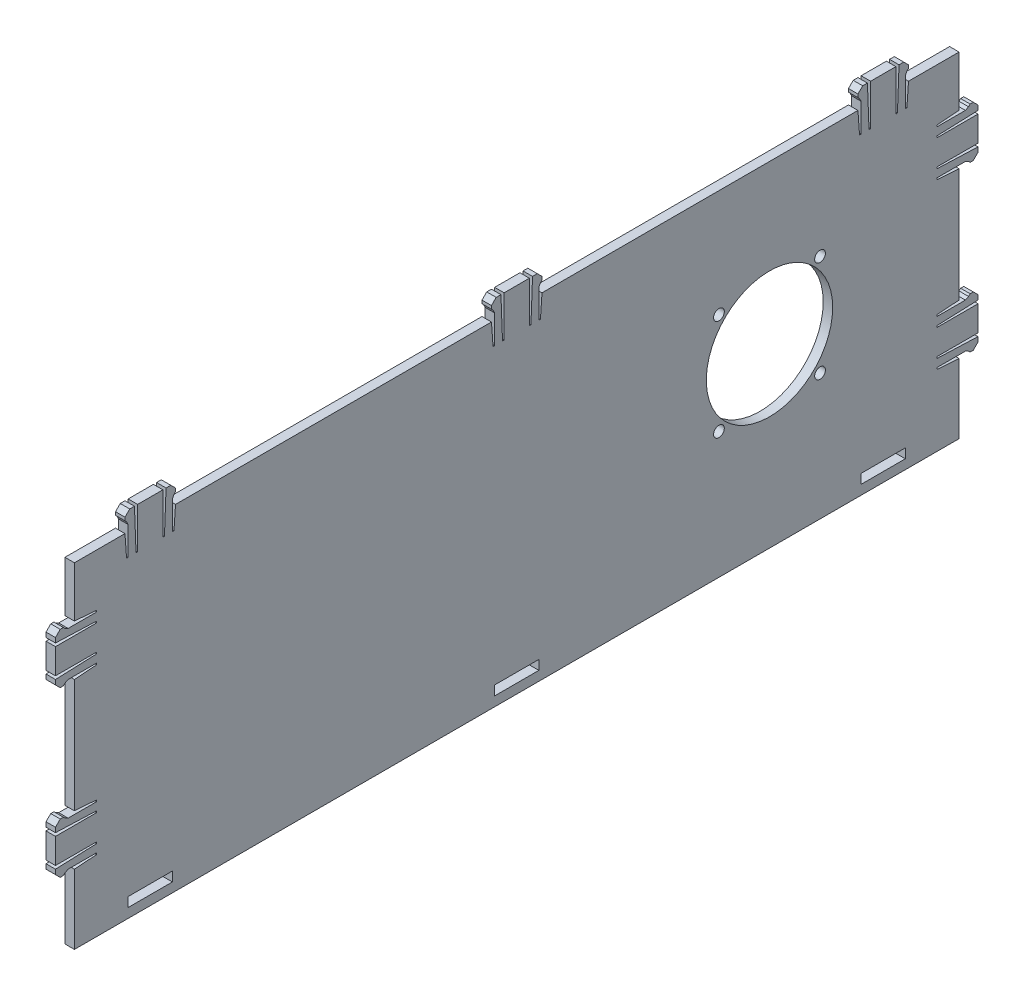
SolidWorks part; units mm, degrees
ref_plane "Front Plane" through (0, 0, 0) normal (0, 0, 1) x (1, 0, 0)
ref_plane "Top Plane" through (0, 0, 0) normal (0, 1, 0) x (1, 0, 0)
ref_plane "Right Plane" through (0, 0, 0) normal (1, 0, 0) x (0, 0, -1)
sketch "Sketch1" plane through (0, 0, 0) normal (1, 0, 0) x (0, 0, -1)
  line L0 (-140, 34) -> (-140, 50)
  line L1 (-124, 50) -> (-140, 50)
  line L2 (-140, -34) -> (-140, -56)
  line L3 (-140, -56) -> (140, -56)
  line L4 (140, 34) -> (140, 50)
  line L5 (-140, 18) -> (-140, -18)
  line L6 (-140, -34) -> (-132.9978, -33.5)
  line L7 (-132.9978, -33.5) -> (-132.9978, -33)
  line L8 (-132.9978, -33) -> (-141.9978, -33)
  line L9 (-141.9978, -33) -> (-142.9978, -33.5)
  line L10 (-142.9978, -33.5) -> (-143.4978, -34)
  line L11 (-143.4978, -34) -> (-144.4978, -34)
  line L12 (-144.4978, -34) -> (-145.9978, -32.5)
  line L13 (-145.9978, -32.5) -> (-145.9978, -31)
  line L14 (-145.9978, -31) -> (-132.9978, -30.5)
  line L15 (-132.9978, -30.5) -> (-132.9978, -30)
  line L16 (-132.9978, -30) -> (-145.9978, -30)
  line L17 (-132.9978, -22) -> (-145.9978, -22)
  line L18 (-132.9978, -21.5) -> (-132.9978, -22)
  line L19 (-145.9978, -21) -> (-132.9978, -21.5)
  line L20 (-145.9978, -19.5) -> (-145.9978, -21)
  line L21 (-144.4978, -18) -> (-145.9978, -19.5)
  line L22 (-143.4978, -18) -> (-144.4978, -18)
  line L23 (-142.9978, -18.5) -> (-143.4978, -18)
  line L24 (-141.9978, -19) -> (-142.9978, -18.5)
  line L25 (-132.9978, -19) -> (-141.9978, -19)
  line L26 (-132.9978, -18.5) -> (-132.9978, -19)
  line L27 (-140, -18) -> (-132.9978, -18.5)
  line L28 (-145.9978, -30) -> (-145.9978, -22)
  line L29 (-140, 18) -> (-132.9978, 18.5)
  line L30 (-132.9978, 18.5) -> (-132.9978, 19)
  line L31 (-132.9978, 19) -> (-141.9978, 19)
  line L32 (-141.9978, 19) -> (-142.9978, 18.5)
  line L33 (-142.9978, 18.5) -> (-143.4978, 18)
  line L34 (-143.4978, 18) -> (-144.4978, 18)
  line L35 (-144.4978, 18) -> (-145.9978, 19.5)
  line L36 (-145.9978, 19.5) -> (-145.9978, 21)
  line L37 (-145.9978, 21) -> (-132.9978, 21.5)
  line L38 (-132.9978, 21.5) -> (-132.9978, 22)
  line L39 (-132.9978, 22) -> (-145.9978, 22)
  line L40 (-132.9978, 30) -> (-145.9978, 30)
  line L41 (-132.9978, 30.5) -> (-132.9978, 30)
  line L42 (-145.9978, 31) -> (-132.9978, 30.5)
  line L43 (-145.9978, 32.5) -> (-145.9978, 31)
  line L44 (-144.4978, 34) -> (-145.9978, 32.5)
  line L45 (-143.4978, 34) -> (-144.4978, 34)
  line L46 (-142.9978, 33.5) -> (-143.4978, 34)
  line L47 (-141.9978, 33) -> (-142.9978, 33.5)
  line L48 (-132.9978, 33) -> (-141.9978, 33)
  line L49 (-132.9978, 33.5) -> (-132.9978, 33)
  line L50 (-140, 34) -> (-132.9978, 33.5)
  line L51 (-145.9978, 22) -> (-145.9978, 30)
  line L52 (140, -34) -> (140, -56)
  line L53 (140, -18) -> (140, 18)
  line L54 (140, 34) -> (132.9978, 33.5)
  line L55 (132.9978, 33.5) -> (132.9978, 33)
  line L56 (132.9978, 33) -> (141.9978, 33)
  line L57 (141.9978, 33) -> (142.9978, 33.5)
  line L58 (142.9978, 33.5) -> (143.4978, 34)
  line L59 (143.4978, 34) -> (144.4978, 34)
  line L60 (144.4978, 34) -> (145.9978, 32.5)
  line L61 (145.9978, 32.5) -> (145.9978, 31)
  line L62 (145.9978, 31) -> (132.9978, 30.5)
  line L63 (132.9978, 30.5) -> (132.9978, 30)
  line L64 (132.9978, 30) -> (145.9978, 30)
  line L65 (132.9978, 22) -> (145.9978, 22)
  line L66 (132.9978, 21.5) -> (132.9978, 22)
  line L67 (145.9978, 21) -> (132.9978, 21.5)
  line L68 (145.9978, 19.5) -> (145.9978, 21)
  line L69 (144.4978, 18) -> (145.9978, 19.5)
  line L70 (143.4978, 18) -> (144.4978, 18)
  line L71 (142.9978, 18.5) -> (143.4978, 18)
  line L72 (141.9978, 19) -> (142.9978, 18.5)
  line L73 (132.9978, 19) -> (141.9978, 19)
  line L74 (132.9978, 18.5) -> (132.9978, 19)
  line L75 (140, 18) -> (132.9978, 18.5)
  line L76 (145.9978, 30) -> (145.9978, 22)
  line L77 (140, -18) -> (132.9978, -18.5)
  line L78 (132.9978, -18.5) -> (132.9978, -19)
  line L79 (132.9978, -19) -> (141.9978, -19)
  line L80 (141.9978, -19) -> (142.9978, -18.5)
  line L81 (142.9978, -18.5) -> (143.4978, -18)
  line L82 (143.4978, -18) -> (144.4978, -18)
  line L83 (144.4978, -18) -> (145.9978, -19.5)
  line L84 (145.9978, -19.5) -> (145.9978, -21)
  line L85 (145.9978, -21) -> (132.9978, -21.5)
  line L86 (132.9978, -21.5) -> (132.9978, -22)
  line L87 (132.9978, -22) -> (145.9978, -22)
  line L88 (132.9978, -30) -> (145.9978, -30)
  line L89 (132.9978, -30.5) -> (132.9978, -30)
  line L90 (145.9978, -31) -> (132.9978, -30.5)
  line L91 (145.9978, -32.5) -> (145.9978, -31)
  line L92 (144.4978, -34) -> (145.9978, -32.5)
  line L93 (143.4978, -34) -> (144.4978, -34)
  line L94 (142.9978, -33.5) -> (143.4978, -34)
  line L95 (141.9978, -33) -> (142.9978, -33.5)
  line L96 (132.9978, -33) -> (141.9978, -33)
  line L97 (132.9978, -33.5) -> (132.9978, -33)
  line L98 (140, -34) -> (132.9978, -33.5)
  line L99 (145.9978, -22) -> (145.9978, -30)
  line L100 (124, 50) -> (140, 50)
  line L101 (-108, 50) -> (-8, 50)
  line L102 (8, 50) -> (108, 50)
  line L103 (-124, 50) -> (-123.5, 42.9978)
  line L104 (-123.5, 42.9978) -> (-123, 42.9978)
  line L105 (-123, 42.9978) -> (-123, 51.9978)
  line L106 (-123, 51.9978) -> (-123.5, 52.9978)
  line L107 (-123.5, 52.9978) -> (-124, 53.4978)
  line L108 (-124, 53.4978) -> (-124, 54.4978)
  line L109 (-124, 54.4978) -> (-122.5, 55.9978)
  line L110 (-122.5, 55.9978) -> (-121, 55.9978)
  line L111 (-121, 55.9978) -> (-120.5, 42.9978)
  line L112 (-120.5, 42.9978) -> (-120, 42.9978)
  line L113 (-120, 42.9978) -> (-120, 55.9978)
  line L114 (-116, 50) -> (-116, 55.7386) construction
  line L115 (-112, 42.9978) -> (-112, 55.9978)
  line L116 (-111.5, 42.9978) -> (-112, 42.9978)
  line L117 (-111, 55.9978) -> (-111.5, 42.9978)
  line L118 (-109.5, 55.9978) -> (-111, 55.9978)
  line L119 (-108, 54.4978) -> (-109.5, 55.9978)
  line L120 (-108, 53.4978) -> (-108, 54.4978)
  line L121 (-108.5, 52.9978) -> (-108, 53.4978)
  line L122 (-109, 51.9978) -> (-108.5, 52.9978)
  line L123 (-109, 42.9978) -> (-109, 51.9978)
  line L124 (-108.5, 42.9978) -> (-109, 42.9978)
  line L125 (-108, 50) -> (-108.5, 42.9978)
  line L126 (-120, 55.9978) -> (-112, 55.9978)
  line L127 (-8, 50) -> (-7.5, 42.9978)
  line L128 (-7.5, 42.9978) -> (-7, 42.9978)
  line L129 (-7, 42.9978) -> (-7, 51.9978)
  line L130 (-7, 51.9978) -> (-7.5, 52.9978)
  line L131 (-7.5, 52.9978) -> (-8, 53.4978)
  line L132 (-8, 53.4978) -> (-8, 54.4978)
  line L133 (-8, 54.4978) -> (-6.5, 55.9978)
  line L134 (-6.5, 55.9978) -> (-5, 55.9978)
  line L135 (-5, 55.9978) -> (-4.5, 42.9978)
  line L136 (-4.5, 42.9978) -> (-4, 42.9978)
  line L137 (-4, 42.9978) -> (-4, 55.9978)
  line L138 (0, 50) -> (0, 55.7386) construction
  line L139 (4, 42.9978) -> (4, 55.9978)
  line L140 (4.5, 42.9978) -> (4, 42.9978)
  line L141 (5, 55.9978) -> (4.5, 42.9978)
  line L142 (6.5, 55.9978) -> (5, 55.9978)
  line L143 (8, 54.4978) -> (6.5, 55.9978)
  line L144 (8, 53.4978) -> (8, 54.4978)
  line L145 (7.5, 52.9978) -> (8, 53.4978)
  line L146 (7, 51.9978) -> (7.5, 52.9978)
  line L147 (7, 42.9978) -> (7, 51.9978)
  line L148 (7.5, 42.9978) -> (7, 42.9978)
  line L149 (8, 50) -> (7.5, 42.9978)
  line L150 (-4, 55.9978) -> (4, 55.9978)
  line L151 (108, 50) -> (108.5, 42.9978)
  line L152 (108.5, 42.9978) -> (109, 42.9978)
  line L153 (109, 42.9978) -> (109, 51.9978)
  line L154 (109, 51.9978) -> (108.5, 52.9978)
  line L155 (108.5, 52.9978) -> (108, 53.4978)
  line L156 (108, 53.4978) -> (108, 54.4978)
  line L157 (108, 54.4978) -> (109.5, 55.9978)
  line L158 (109.5, 55.9978) -> (111, 55.9978)
  line L159 (111, 55.9978) -> (111.5, 42.9978)
  line L160 (111.5, 42.9978) -> (112, 42.9978)
  line L161 (112, 42.9978) -> (112, 55.9978)
  line L162 (116, 50) -> (116, 55.7386) construction
  line L163 (120, 42.9978) -> (120, 55.9978)
  line L164 (120.5, 42.9978) -> (120, 42.9978)
  line L165 (121, 55.9978) -> (120.5, 42.9978)
  line L166 (122.5, 55.9978) -> (121, 55.9978)
  line L167 (124, 54.4978) -> (122.5, 55.9978)
  line L168 (124, 53.4978) -> (124, 54.4978)
  line L169 (123.5, 52.9978) -> (124, 53.4978)
  line L170 (123, 51.9978) -> (123.5, 52.9978)
  line L171 (123, 42.9978) -> (123, 51.9978)
  line L172 (123.5, 42.9978) -> (123, 42.9978)
  line L173 (124, 50) -> (123.5, 42.9978)
  line L174 (112, 55.9978) -> (120, 55.9978)
  point P12 (-140, -34)
  point P37 (-140, 18)
  point P61 (140, 34)
  point P62 (140, 18)
  point P63 (140, 18)
  point P86 (140, -18)
  point P87 (140, -34)
  point P88 (140, -34)
  point P117 (-124, 50)
  point P143 (-8, 50)
  point P168 (108, 50)
  dimension "D1" = 280
  dimension "D2" = 106
  dimension "D3" = 140
  dimension "D4" = 50
  dimension "D5" = 16
  dimension "D6" = 36
  dimension "D7" = 7.0022
  dimension "D8" = 0.5
  dimension "D9" = 0.5
  dimension "D10" = 9
  dimension "D11" = 1
  dimension "D12" = 0.5
  dimension "D13" = 0.5
  dimension "D14" = 0.5
  dimension "D15" = 1
  dimension "D16" = 1.5
  dimension "D17" = 1.5
  dimension "D18" = 1.5
  dimension "D19" = 13
  dimension "D20" = 0.5
  dimension "D21" = 0.5
  dimension "D22" = 13
  dimension "D23" = 8
  dimension "D24" = 13
  dimension "D25" = 0.5
  dimension "D26" = 13
  dimension "D27" = 0.5
  dimension "D28" = 1.5
  dimension "D29" = 1.5
  dimension "D30" = 1.5
  dimension "D31" = 1
  dimension "D32" = 0.5
  dimension "D33" = 0.5
  dimension "D34" = 1
  dimension "D35" = 0.5
  dimension "D36" = 9
  dimension "D37" = 0.5
  dimension "D38" = 7.0022
  dimension "D39" = 0.5
  dimension "D40" = 7.0022
  dimension "D41" = 0.5
  dimension "D42" = 0.5
  dimension "D43" = 9
  dimension "D44" = 1
  dimension "D45" = 0.5
  dimension "D46" = 0.5
  dimension "D47" = 0.5
  dimension "D48" = 1
  dimension "D49" = 1.5
  dimension "D50" = 1.5
  dimension "D51" = 1.5
  dimension "D52" = 13
  dimension "D53" = 0.5
  dimension "D54" = 0.5
  dimension "D55" = 13
  dimension "D56" = 8
  dimension "D57" = 13
  dimension "D58" = 0.5
  dimension "D59" = 13
  dimension "D60" = 0.5
  dimension "D61" = 1.5
  dimension "D62" = 1.5
  dimension "D63" = 1.5
  dimension "D64" = 1
  dimension "D65" = 0.5
  dimension "D66" = 0.5
  dimension "D67" = 1
  dimension "D68" = 0.5
  dimension "D69" = 9
  dimension "D70" = 0.5
  dimension "D71" = 7.0022
  dimension "D72" = 0.5
  dimension "D73" = 16
  dimension "D74" = 36
  dimension "D75" = 7.0022
  dimension "D76" = 0.5
  dimension "D77" = 0.5
  dimension "D78" = 9
  dimension "D79" = 1
  dimension "D80" = 0.5
  dimension "D81" = 0.5
  dimension "D82" = 0.5
  dimension "D83" = 1
  dimension "D84" = 1.5
  dimension "D85" = 1.5
  dimension "D86" = 1.5
  dimension "D87" = 13
  dimension "D88" = 0.5
  dimension "D89" = 0.5
  dimension "D90" = 13
  dimension "D91" = 8
  dimension "D92" = 13
  dimension "D93" = 0.5
  dimension "D94" = 13
  dimension "D95" = 1.5
  dimension "D96" = 1.5
  dimension "D97" = 1.5
  dimension "D98" = 1
  dimension "D99" = 0.5
  dimension "D100" = 0.5
  dimension "D101" = 1
  dimension "D102" = 0.5
  dimension "D103" = 9
  dimension "D104" = 0.5
  dimension "D105" = 7.0022
  dimension "D106" = 0.5
  dimension "D107" = 7.0022
  dimension "D108" = 0.5
  dimension "D109" = 0.5
  dimension "D110" = 9
  dimension "D111" = 1
  dimension "D112" = 0.5
  dimension "D113" = 0.5
  dimension "D114" = 0.5
  dimension "D115" = 1
  dimension "D116" = 1.5
  dimension "D117" = 1.5
  dimension "D118" = 1.5
  dimension "D119" = 13
  dimension "D120" = 0.5
  dimension "D121" = 0.5
  dimension "D122" = 13
  dimension "D123" = 8
  dimension "D124" = 13
  dimension "D125" = 0.5
  dimension "D126" = 13
  dimension "D127" = 1.5
  dimension "D128" = 1.5
  dimension "D129" = 1.5
  dimension "D130" = 1
  dimension "D131" = 0.5
  dimension "D132" = 0.5
  dimension "D133" = 1
  dimension "D134" = 0.5
  dimension "D135" = 9
  dimension "D136" = 0.5
  dimension "D137" = 7.0022
  dimension "D138" = 0.5
  dimension "D139" = 22
  dimension "D140" = 0.5
  dimension "D141" = 16
  dimension "D142" = 100
  dimension "D143" = 100
  dimension "D144" = 0.5
  dimension "D145" = 9
  dimension "D146" = 0.5
  dimension "D147" = 1
  dimension "D148" = 0.5
  dimension "D149" = 0.5
  dimension "D150" = 1
  dimension "D151" = 1.5
  dimension "D152" = 1.5
  dimension "D153" = 0.5
  dimension "D154" = 0.5
  dimension "D155" = 13
  dimension "D156" = 7.0022
  dimension "D157" = 1.5
  dimension "D158" = 13
  dimension "D159" = 8
  dimension "D160" = 8
  dimension "D161" = 0.5
  dimension "D162" = 9
  dimension "D163" = 0.5
  dimension "D164" = 1
  dimension "D165" = 0.5
  dimension "D166" = 0.5
  dimension "D167" = 1
  dimension "D168" = 1.5
  dimension "D169" = 1.5
  dimension "D170" = 0.5
  dimension "D171" = 0.5
  dimension "D172" = 13
  dimension "D173" = 7.0022
  dimension "D174" = 1.5
  dimension "D175" = 13
  dimension "D176" = 8
  dimension "D177" = 8
  dimension "D178" = 0.5
  dimension "D179" = 9
  dimension "D180" = 0.5
  dimension "D181" = 1
  dimension "D182" = 0.5
  dimension "D183" = 0.5
  dimension "D184" = 1
  dimension "D185" = 1.5
  dimension "D186" = 1.5
  dimension "D187" = 0.5
  dimension "D188" = 0.5
  dimension "D189" = 13
  dimension "D190" = 7.0022
  dimension "D191" = 1.5
  dimension "D192" = 13
  dimension "D193" = 8
  dimension "D194" = 8
  dimension "D195" = 7.02
  dimension "D196" = 7.02
  dimension "D197" = 0.5
extrude "Boss-Extrude1" add sketch "Sketch1" along normal blind 3
sketch "Sketch3" plane through (3, 0, 0) normal (1, 0, 0) x (0, 0, -1)
  line L1 (-123, -50) -> (-109, -50)
  line L2 (-123, -50) -> (-123, -53)
  line L3 (-123, -53) -> (-109, -53)
  line L4 (-109, -50) -> (-109, -53)
  line L5 (-7, -50) -> (7, -50)
  line L6 (-7, -50) -> (-7, -53)
  line L7 (-7, -53) -> (7, -53)
  line L8 (7, -50) -> (7, -53)
  line L9 (123, -50) -> (109, -50)
  line L10 (123, -50) -> (123, -53)
  line L11 (123, -53) -> (109, -53)
  line L12 (109, -50) -> (109, -53)
  dimension "D1" = 14
  dimension "D2" = 3
  dimension "D3" = 109
  dimension "D4" = 50
  dimension "D5" = 14
  dimension "D6" = 3
  dimension "D7" = 50
  dimension "D8" = 7
  dimension "D9" = 14
  dimension "D10" = 3
  dimension "D11" = 50
  dimension "D12" = 109
extrude "Cut-Extrude1" cut sketch "Sketch3" against normal blind 3
sketch "Sketch6" plane through (3, 0, 0) normal (1, 0, 0) x (0, 0, -1)
  text T1 "BOXZ1" font "Century Gothic" height in points 22
  dimension "D1" = 11.2
  dimension "D2" = 0
sketch "Sketch7" plane through (3, 0, 0) normal (1, 0, 0) x (0, 0, -1)
  circle A0 centre (80, 0) radius 20
  dimension "D1" = 40
  dimension "D2" = 80
  dimension "D3" = 50
extrude "Cut-Extrude2" cut sketch "Sketch7" against normal blind 3
sketch "Sketch9" plane through (3, 0, 0) normal (1, 0, 0) x (0, 0, -1)
  circle A0 centre (64, 16) radius 1.7
  circle A1 centre (96, 16) radius 1.7
  circle A2 centre (96, -16) radius 1.7
  circle A3 centre (64, -16) radius 1.7
  point P0 (80, 0)
  dimension "D1" = 3.4
  dimension "D2" = 3.4
  dimension "D3" = 3.4
  dimension "D4" = 3.4
  dimension "D5" = 16
  dimension "D6" = 16
  dimension "D7" = 16
  dimension "D8" = 16
  dimension "D9" = 16
  dimension "D10" = 16
  dimension "D11" = 16
  dimension "D12" = 16
extrude "Cut-Extrude3" cut sketch "Sketch9" against normal blind 3
